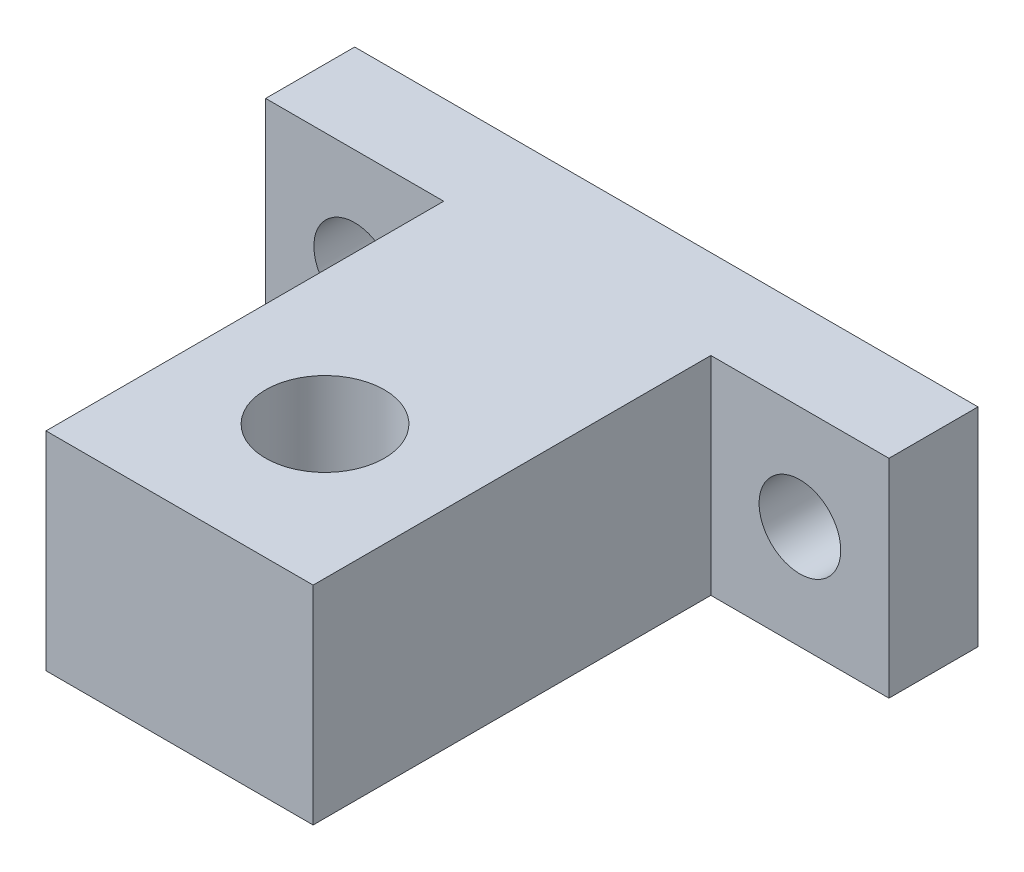
SolidWorks part; units mm, degrees
ref_plane "Top Plane" through (0, 0, 0) normal (0, 0, 1) x (1, 0, 0)
ref_plane "Front Plane" through (0, 0, 0) normal (0, 1, 0) x (1, 0, 0)
ref_plane "Right Plane" through (0, 0, 0) normal (1, 0, 0) x (0, 0, -1)
sketch "Profile Sketch" plane through (0, 0, 0) normal (0, 1, 0) x (1, 0, 0)
  line L0 (9, -3) -> (21, -3)
  line L1 (-21, -3) -> (-9, -3)
  line L2 (-21, -3) -> (-21, 3)
  line L3 (-21, 3) -> (21, 3)
  line L4 (21, -3) -> (21, 3)
  line L5 (-21, -3) -> (21, 3) construction
  line L6 (-21, 3) -> (21, -3) construction
  line L7 (-9, -29.8) -> (9, -29.8)
  line L8 (-9, -29.8) -> (-9, -3)
  line L10 (9, -29.8) -> (9, -3)
  line L11 (-9, -29.8) -> (9, -3) construction
  line L12 (-9, -3) -> (9, -29.8) construction
  point P0 (0, 0)
  point P6 (0, -16.4)
  dimension "D1" = 42
  dimension "D2" = 18
  dimension "D3" = 6
  dimension "D4" = 32.8
extrude "Profile Extrude" add sketch "Profile Sketch" along normal blind 14 contours L8 L1 L2 L3 L4 L0 L10 L7
sketch "Bore Sketch" plane through (0, 0, 0) normal (0, -1, 0) x (1, 0, 0)
  circle A0 centre (0, 20) radius 4
  dimension "D1" = 8
  dimension "D2" = 20
extrude "Bore Cut" cut sketch "Bore Sketch" against normal through all
sketch "Mounting Hole Sketch" plane through (0, 0, 3) normal (0, 0, 1) x (1, 0, 0)
  line L0 (15, 14) -> (15, 0) construction
  line L1 (9, 14) -> (21, 14) construction
  line L2 (9, 0) -> (21, 0) construction
  line L4 (-15, 14) -> (-15, 0) construction
  line L5 (-21, 14) -> (-9, 14) construction
  line L6 (-21, 0) -> (-9, 0) construction
  circle A0 centre (15, 7) radius 2.75
  circle A1 centre (-15, 7) radius 2.75
  dimension "D1" = 5.5
  dimension "D2" = 5.5
extrude "Mounting Hole Cut" cut sketch "Mounting Hole Sketch" against normal through all
